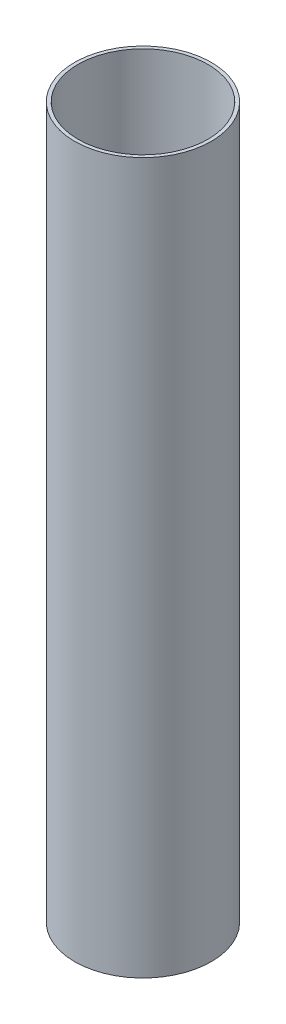
SolidWorks part; units mm, degrees
material "75mm-Phenolic Liner"
ref_plane "Front Plane" through (0, 0, 0) normal (0, 0, 1) x (1, 0, 0)
ref_plane "Top Plane" through (0, 0, 0) normal (0, 1, 0) x (1, 0, 0)
ref_plane "Right Plane" through (0, 0, 0) normal (1, 0, 0) x (0, 0, -1)
sketch "Sketch1" plane through (0, 0, 0) normal (0, 1, 0) x (1, 0, 0)
  circle A0 centre (0, 0) radius 33.147
  circle A1 centre (0, 0) radius 34.8996
  dimension "D1" = 66.294
  dimension "D2" = 69.7992
extrude "Boss-Extrude1" add sketch "Sketch1" along normal blind 362.585
